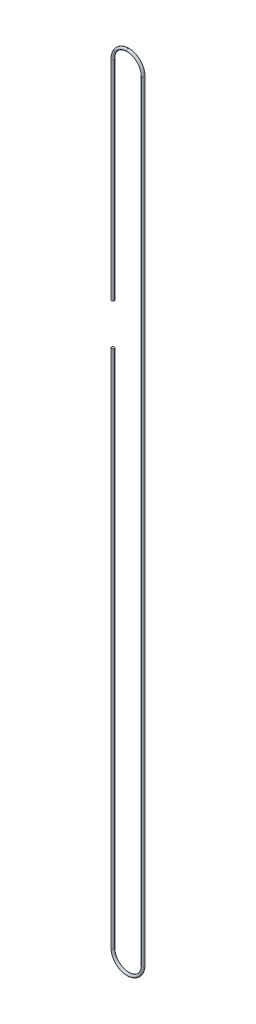
SolidWorks part; units mm, degrees
material "Nylon 101"
ref_plane "Front Plane" through (0, 0, 0) normal (0, 0, 1) x (1, 0, 0)
ref_plane "Top Plane" through (0, 0, 0) normal (0, 1, 0) x (1, 0, 0)
ref_plane "Right Plane" through (0, 0, 0) normal (1, 0, 0) x (0, 0, -1)
sketch "Sketch1" plane through (0, 0, 0) normal (0, 0, 1) x (1, 0, 0)
  line L0 (-17.4625, 889) -> (-17.4625, 0)
  line L1 (17.4625, 889) -> (17.4625, 0)
  circle A0 centre (0, 0) radius 17.4625 construction
  circle A1 centre (0, 889) radius 17.4625 construction
  arc A2 (-17.4625, 889) -> (17.4625, 889) centre (0, 889) cw
  arc A3 (-17.4625, 0) -> (17.4625, 0) centre (0, 0) ccw
  dimension "D2" = 17.4625
  dimension "D1" = 889
sketch "Sketch2" plane through (0, 0, 0) normal (1, 0, 0) x (0, 0, -1)
  line L0 (0, 906.4625) -> (0, 889) construction
  line L1 (0, 906.4625) -> (0, 889) construction
  circle A0 centre (0, 906.4625) radius 1.5875
  dimension "D1" = 3.175
sweep "Sweep1" add profiles "Sketch2" path "Sketch1"
sketch "Sketch3" plane through (0, 0, 0) normal (0, 0, 1) x (1, 0, 0)
  line L1 (-38.2585, 647.7) -> (-2.2207, 647.7)
  line L2 (-38.2585, 647.7) -> (-38.2585, 600.075)
  line L3 (-38.2585, 600.075) -> (-2.2207, 600.075)
  line L4 (-2.2207, 647.7) -> (-2.2207, 600.075)
  dimension "D1" = 47.625
  dimension "D2" = 241.3
extrude "Cut-Extrude1" cut sketch "Sketch3" against normal through all both and the other way through all
